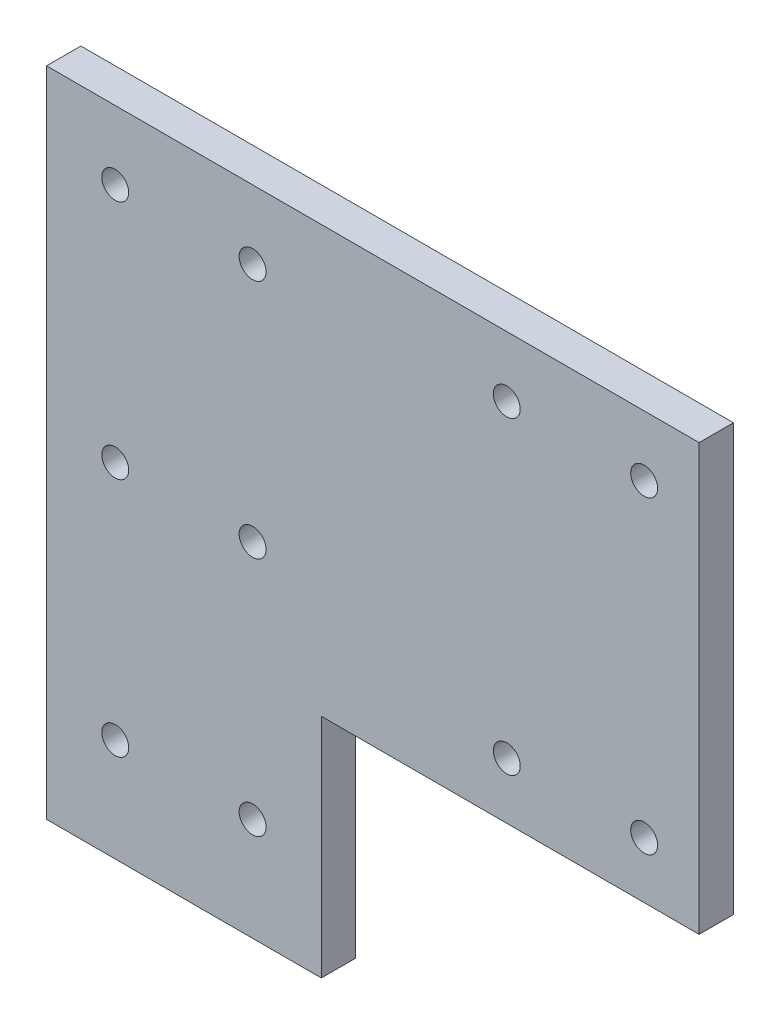
SolidWorks part; units mm, degrees
material "6061-T6 (SS)"
ref_plane "Front Plane" through (0, 0, 0) normal (0, 0, 1) x (1, 0, 0)
ref_plane "Top Plane" through (0, 0, 0) normal (0, 1, 0) x (1, 0, 0)
ref_plane "Right Plane" through (0, 0, 0) normal (1, 0, 0) x (0, 0, -1)
sketch "Sketch1" plane through (0, 0, 0) normal (0, 0, 1) x (1, 0, 0)
  line L0 (0, 0) -> (0, 120.65)
  line L1 (0, 120.65) -> (120.65, 120.65)
  line L2 (120.65, 120.65) -> (120.65, 41.91)
  line L3 (120.65, 41.91) -> (50.8, 41.91)
  line L4 (50.8, 41.91) -> (50.8, 0)
  line L5 (50.8, 0) -> (0, 0)
  dimension "D1" = 120.65
  dimension "D2" = 50.8
  dimension "D3" = 78.74
  dimension "D4" = 69.85
extrude "Boss-Extrude1" add sketch "Sketch1" along normal blind 6.35
sketch "Sketch2" plane through (0, 0, 0) normal (0, 0, -1) x (-1, 0, 0)
  line L1 (-110.49, 52.324) -> (-85.09, 52.324) construction
  line L2 (-110.49, 52.324) -> (-110.49, 109.474) construction
  line L3 (-110.49, 109.474) -> (-85.09, 109.474) construction
  line L4 (-85.09, 52.324) -> (-85.09, 109.474) construction
  line L5 (-110.49, 52.324) -> (-85.09, 109.474) construction
  line L6 (-110.49, 109.474) -> (-85.09, 52.324) construction
  line L7 (-120.65, 120.65) -> (0, 120.65) construction
  line L8 (-120.65, 41.91) -> (-120.65, 120.65) construction
  line L9 (0, 0) -> (-50.8, 0) construction
  line L10 (-38.1, 19.05) -> (-12.7, 19.05) construction
  line L11 (-38.1, 19.05) -> (-38.1, 107.95) construction
  line L12 (-38.1, 107.95) -> (-12.7, 107.95) construction
  line L13 (-12.7, 19.05) -> (-12.7, 107.95) construction
  line L14 (-50.8, 0) -> (-50.8, 41.91) construction
  line L16 (0, 120.65) -> (0, 0) construction
  circle A0 centre (-110.49, 109.474) radius 2.4892
  circle A1 centre (-85.09, 109.474) radius 2.4892
  circle A2 centre (-85.09, 52.324) radius 2.4892
  circle A3 centre (-110.49, 52.324) radius 2.4892
  circle A4 centre (-38.1, 107.95) radius 2.4892
  circle A5 centre (-12.7, 107.95) radius 2.4892
  circle A6 centre (-12.7, 19.05) radius 2.4892
  circle A7 centre (-38.1, 19.05) radius 2.4892
  circle A8 centre (-38.1, 63.5) radius 2.4892
  circle A9 centre (-12.7, 63.5) radius 2.4892
  point P0 (-97.79, 80.899)
  point P27 (-25.4, 107.95)
  dimension "D3" = 4.9784
  dimension "D6" = 4.9784
  dimension "D1" = 25.4
  dimension "D2" = 57.15
  dimension "D4" = 11.176
  dimension "D5" = 10.16
  dimension "D7" = 19.05
  dimension "D8" = 12.7
  dimension "D9" = 12.7
  dimension "D10" = 12.7
extrude "Cut-Extrude1" cut sketch "Sketch2" against normal through all
